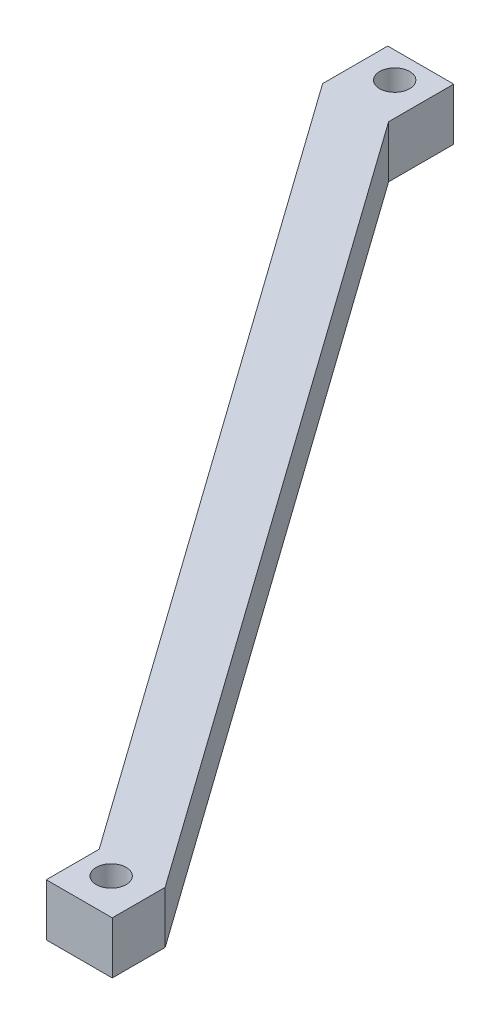
SolidWorks part; units mm, degrees
ref_plane "Front Plane" through (0, 0, 0) normal (0, 0, 1) x (1, 0, 0)
ref_plane "Top Plane" through (0, 0, 0) normal (0, 1, 0) x (1, 0, 0)
ref_plane "Right Plane" through (0, 0, 0) normal (1, 0, 0) x (0, 0, -1)
sketch "Sketch2" plane through (0, 0, 0) normal (0, 1, 0) x (1, 0, 0)
  line L0 (0, 0) -> (223.5165, -331.7234) construction
  line L1 (-12.6662, 10) -> (-12.6662, -15)
  line L2 (-12.6662, -15) -> (198.9571, -312.3896)
  line L3 (198.9571, -312.3896) -> (198.9571, -332.6982)
  line L4 (198.9571, -332.6982) -> (224.2894, -332.6982)
  line L5 (224.2894, -332.6982) -> (224.2894, -312.3896)
  line L6 (224.2894, -312.3896) -> (12.6662, -15)
  line L7 (12.6662, -15) -> (12.6662, 10)
  line L8 (12.6662, 10) -> (-12.6662, 10)
  point P5 (0, 10)
  point P12 (0, 0)
  dimension "D1" = 400
  dimension "D2" = 25
  dimension "D3" = 15
  dimension "D4" = 365
extrude "Boss-Extrude2" add sketch "Sketch2" along normal blind 20
sketch "Sketch3" plane through (0, 20, 0) normal (0, 1, 0) x (1, 0, 0)
  circle A0 centre (0, 0) radius 5.75
  circle A1 centre (210.1647, -318.9903) radius 5.75
  dimension "D1" = 11.5
  dimension "D2" = 11.5
  dimension "D3" = 382
extrude "Cut-Extrude1" cut sketch "Sketch3" against normal through all
